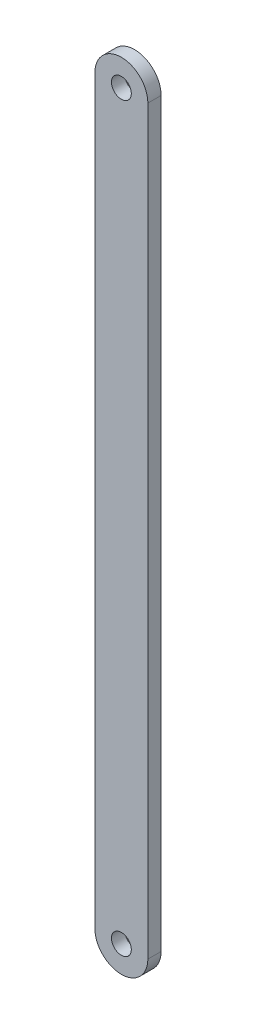
SolidWorks part; units mm, degrees
ref_plane "Front Plane" through (0, 0, 0) normal (0, 0, 1) x (1, 0, 0)
ref_plane "Top Plane" through (0, 0, 0) normal (0, 1, 0) x (1, 0, 0)
ref_plane "Right Plane" through (0, 0, 0) normal (1, 0, 0) x (0, 0, -1)
sketch "Sketch1" plane through (0, 0, 0) normal (0, 0, 1) x (1, 0, 0)
  line L0 (0, 96.5) -> (0, -30.5) construction
  line L2 (-4, 96.5) -> (-4, -15.5)
  line L4 (4, 96.5) -> (4, -15.5)
  circle A0 centre (0, 96.5) radius 1.5
  arc A1 (4, 96.5) -> (-4, 96.5) centre (0, 96.5) ccw
  circle A2 centre (0, -15.5) radius 1.5
  arc A4 (-4, -15.5) -> (4, -15.5) centre (0, -15.5) ccw
  point P0 (0, 0)
  dimension "D3" = 3
  dimension "D4" = 112
  dimension "D1" = 4
  dimension "D2" = 4
extrude "Boss-Extrude1" add sketch "Sketch1" along normal blind 2
